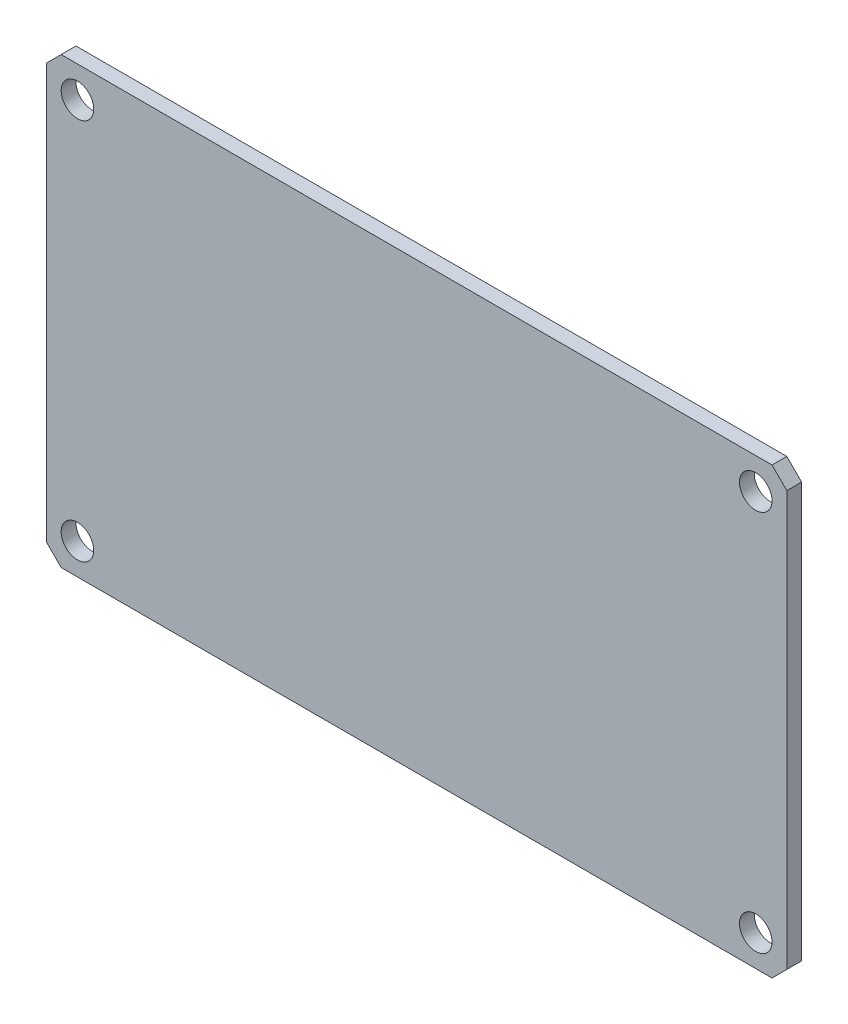
SolidWorks part; units mm, degrees
ref_plane "Front Plane" through (0, 0, 0) normal (0, 0, 1) x (1, 0, 0)
ref_plane "Top Plane" through (0, 0, 0) normal (0, 1, 0) x (1, 0, 0)
ref_plane "Right Plane" through (0, 0, 0) normal (1, 0, 0) x (0, 0, -1)
sketch "Sketch1" plane through (0, 0, 0) normal (0, 0, 1) x (1, 0, 0)
  line L1 (-37.5, 22.5) -> (37.5, 22.5)
  line L2 (-37.5, 22.5) -> (-37.5, -22.5)
  line L3 (-37.5, -22.5) -> (37.5, -22.5)
  line L4 (37.5, 22.5) -> (37.5, -22.5)
  line L5 (-37.5, 22.5) -> (37.5, -22.5) construction
  line L6 (-37.5, -22.5) -> (37.5, 22.5) construction
  point P0 (0, 0)
  dimension "D1" = 45
  dimension "D2" = 75
extrude "Boss-Extrude1" add sketch "Sketch1" along normal blind 1.5
sketch "Sketch2" plane through (0, 0, 1.5) normal (0, 0, 1) x (1, 0, 0)
  line L0 (0, 0) -> (0, 22.5) construction
  line L1 (37.5, 22.5) -> (-37.5, 22.5) construction
  line L2 (0, 0) -> (-37.5, 0) construction
  line L3 (-37.5, 22.5) -> (-37.5, -22.5) construction
  line L4 (-47.7522, 21) -> (-36, 21) construction
  line L5 (-36, 21) -> (-36, 20.4546) construction
  line L6 (-37.5, 22.5) -> (-36, 22.5)
  line L7 (-36, 22.5) -> (-37.5, 21)
  line L8 (-37.5, 21) -> (-37.5, 22.5)
  line L9 (-43.0111, 13.0223) -> (-40.9426, 15.0908) construction
  line L10 (37.5, 22.5) -> (36, 22.5)
  line L11 (37.5, 21) -> (37.5, 22.5)
  line L12 (36, 22.5) -> (37.5, 21)
  line L13 (37.5, -21) -> (37.5, -22.5)
  line L14 (37.5, -22.5) -> (36, -22.5)
  line L15 (36, -22.5) -> (37.5, -21)
  line L16 (-37.5, -22.5) -> (-36, -22.5)
  line L17 (-37.5, -21) -> (-37.5, -22.5)
  line L18 (-36, -22.5) -> (-37.5, -21)
  circle A0 centre (-34.35, 19.35) radius 1.65
  circle A1 centre (34.35, 19.35) radius 1.65
  circle A2 centre (34.35, -19.35) radius 1.65
  circle A3 centre (-34.35, -19.35) radius 1.65
  circle A4 centre (-34.35, 19.35) radius 3 construction
  point P36 (-55.3837, 27.253)
  dimension "D1" = 3.3
  dimension "D2" = 1.5
  dimension "D6" = 6
  dimension "D3" = 1.5
  dimension "D4" = 1.5
  dimension "D5" = 1.7441
extrude "Cut-Extrude1" cut sketch "Sketch2" against normal through all
